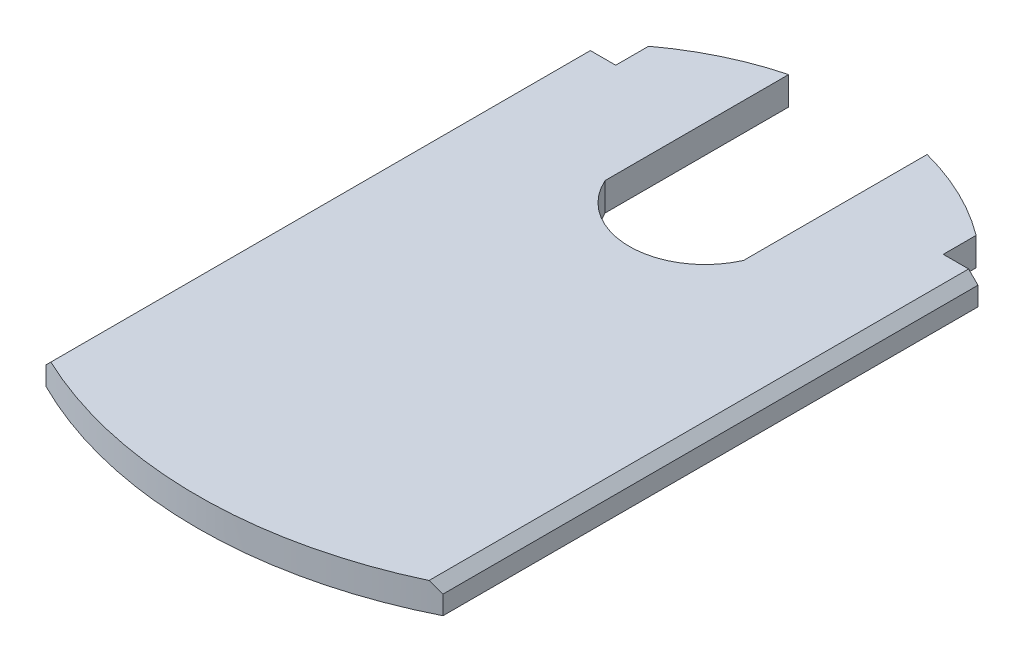
SolidWorks part; units mm, degrees
ref_plane "Front Plane" through (0, 0, 0) normal (0, 0, 1) x (1, 0, 0)
ref_plane "Top Plane" through (0, 0, 0) normal (0, 1, 0) x (1, 0, 0)
ref_plane "Right Plane" through (0, 0, 0) normal (1, 0, 0) x (0, 0, -1)
sketch "Sketch1" plane through (0, 0, 0) normal (0, 1, 0) x (1, 0, 0)
  line L0 (-17.45, 28.5) -> (-17.45, 32)
  line L5 (-21.15, 28.5) -> (21.15, 28.5)
  line L6 (-21.15, 28.5) -> (-21.15, -28.5)
  line L7 (-21.15, -28.5) -> (21.15, -28.5) construction
  line L8 (21.15, 28.5) -> (21.15, -28.5)
  line L9 (-21.15, 28.5) -> (21.15, -28.5) construction
  line L10 (-21.15, -28.5) -> (21.15, 28.5) construction
  line L11 (-17.45, 32) -> (17.45, 32) construction
  line L12 (17.45, 32) -> (17.45, 28.5)
  line L13 (0, 32) -> (0, 28.5) construction
  arc A0 (-21.15, -28.5) -> (21.15, -28.5) centre (0, 13.7322) ccw
  arc A1 (-17.45, 32) -> (17.45, 32) centre (0, 8.6498) cw
  point P0 (0, 0)
  point P14 (0, -33.5)
  point P15 (0, 37.8)
  dimension "D6" = 5.8
  dimension "D1" = 42.3
  dimension "D2" = 57
  dimension "D3" = 34.9
  dimension "D4" = 3.5
  dimension "D5" = 5
extrude "Boss-Extrude1" add sketch "Sketch1" along normal blind 3 contours L6 A0 L8 L5 | A1 L0 L5 L12
sketch "Sketch2" plane through (0, 3, 0) normal (0, 1, 0) x (1, 0, 0)
  line L0 (0, 37.8) -> (0, 17.3) construction
  line L1 (7.375, 17.3) -> (-7.375, 17.3) construction
  line L2 (-7.375, 17.3) -> (-7.375, 37.8)
  line L3 (-7.375, 37.8) -> (7.375, 37.8)
  line L4 (7.375, 17.3) -> (7.375, 37.8)
  line L6 (-21.15, 28.5) -> (-21.15, -28.5)
  line L7 (21.15, -28.5) -> (21.15, 28.5)
  line L8 (21.15, 28.5) -> (17.45, 28.5)
  line L9 (17.45, 28.5) -> (17.45, 32)
  line L10 (-17.45, 32) -> (-17.45, 28.5)
  line L11 (-17.45, 28.5) -> (-21.15, 28.5)
  line L12 (-21.15, 28.5) -> (-21.15, -28.5) construction
  line L13 (21.15, -28.5) -> (21.15, 28.5) construction
  line L14 (21.15, 28.5) -> (17.45, 28.5) construction
  line L15 (17.45, 28.5) -> (17.45, 32) construction
  line L16 (-17.45, 32) -> (-17.45, 28.5) construction
  line L17 (-17.45, 28.5) -> (-21.15, 28.5) construction
  arc A0 (-7.375, 17.3) -> (7.375, 17.3) centre (0, 20.5657) ccw
  arc A2 (-21.15, -28.5) -> (21.15, -28.5) centre (0, 13.7322) ccw
  arc A3 (17.45, 32) -> (-17.45, 32) centre (0, 8.6498) ccw
  arc A4 (-21.15, -28.5) -> (21.15, -28.5) centre (0, 13.7322) ccw construction
  arc A5 (17.45, 32) -> (-17.45, 32) centre (0, 8.6498) ccw construction
  point P17 (0, 12.5)
  dimension "D4" = 4.8
  dimension "D2" = 7.375
  dimension "D3" = 20.5
  dimension "D1" = 0
extrude "Cut-Extrude1" cut sketch "Sketch2" against normal up to surface (3 mm away) up to face at (0, 0, -15.225)
sketch "Sketch5" plane through (0, 3, 0) normal (0, 1, 0) x (1, 0, 0)
  line L0 (0, 37.551) -> (0, -33.5) construction
  line L2 (10, 2.0255) -> (-10, 2.0255)
  arc A0 (-21.15, -28.5) -> (21.15, -28.5) centre (0, 13.7322) ccw construction
  point P10 (0, 0)
  point P12 (0, 2.0255)
hole_wizard "CSK for M3 Flat Head Machine Screw4" positions "3DSketch2" profile "Sketch11" countersink size "M3" standard "ANSI Metric"
sketch3d "3DSketch2"
  point P0 (-10, 3, -2.0255)
  point P3 (10, 3, -2.0255)
sketch "Sketch11" plane through (-10, 3, -2.0255) normal (1, 0, 0) x (0, 0, 1)
  line L0 (0, 0) -> (0, 3)
  line L1 (0, 3) -> (1.7, 3)
  line L2 (1.7, 3) -> (1.7, 1.45)
  line L3 (1.7, 1.45) -> (3.15, 0)
  line L5 (3.15, 0) -> (0, 0)
  line L6 (-1.7, 1.45) -> (-3.15, 0) construction
  line L11 (0, -6.35) -> (0, 107.95) construction
  dimension "Thru Hole Dia." = 3.4
  dimension "Thru Hole Depth" = 3
  dimension "Near C'Sink Dia." = 6.3
  dimension "Near C'Sink Angle" = 90
chamfer "Chamfer1" distance 1 angle 45 2 edges at (21.15, 3, 0) (-21.15, 3, 0)
